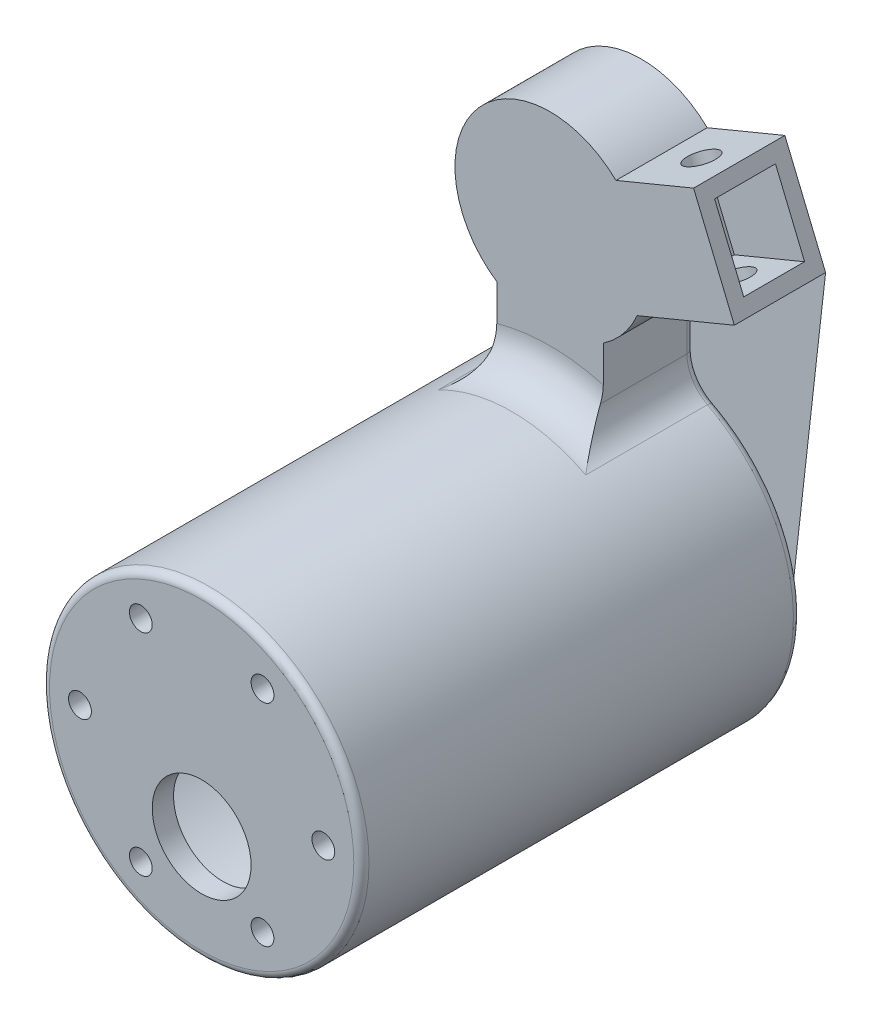
SolidWorks part; units mm, degrees
ref_plane "Front Plane" through (0, 0, 0) normal (0, 0, 1) x (1, 0, 0)
ref_plane "Top Plane" through (0, 0, 0) normal (0, 1, 0) x (1, 0, 0)
ref_plane "Right Plane" through (0, 0, 0) normal (1, 0, 0) x (0, 0, -1)
sketch "Sketch1" plane through (0, 0, 0) normal (0, 0, 1) x (1, 0, 0)
  line L0 (0, 0) -> (-12.5, 0) construction
  line L1 (0, 0) -> (-11.5485, -4.7835) construction
  line L2 (24.2314, 0.2955) -> (11.4585, -4.9953)
  line L3 (0, 0) -> (0, 10) construction
  line L4 (20.7873, 8.6104) -> (24.2314, 0.2955)
  line L5 (20.7873, 8.6104) -> (18.8739, 13.2298)
  line L6 (18.8739, 13.2298) -> (8.671, 9.0036)
  line L8 (0, 0) -> (0, -15.9469) construction
  line L9 (0, -15.9469) -> (-7, -15.9469) construction
  line L12 (-20.7873, -8.6104) -> (-11.5485, -4.7835) construction
  line L15 (0, -15.9469) -> (7, -15.9469) construction
  line L16 (-20.7873, 8.6104) -> (-18.8739, 13.2298)
  line L17 (7, -10.3562) -> (7, -20.3562)
  line L18 (7, -20.3562) -> (-7, -20.3562)
  line L19 (-7, -20.3562) -> (-7, -10.3562)
  line L20 (-18.8739, 13.2298) -> (-8.671, 9.0036)
  line L21 (-20.7873, 8.6104) -> (-24.2314, 0.2955)
  line L22 (-24.2314, 0.2955) -> (-11.4585, -4.9953)
  circle A3 centre (0, 0) radius 12.5
  circle A4 centre (0, 0) radius 10
  dimension "D1" = 25
  dimension "D3" = 22.5
  dimension "D2" = 20
  dimension "D4" = 10
  dimension "D5" = 14
  dimension "D6" = 10
extrude "Boss-Extrude2" add sketch "Sketch1" along normal blind 12 contours A3
sketch "Sketch2" plane through (0, 0, 0) normal (0, 0, 1) x (1, 0, 0)
  line L0 (24.2314, 0.2955) -> (11.4585, -4.9953) construction
  line L1 (20.7873, 8.6104) -> (24.2314, 0.2955) construction
  line L2 (20.7873, 8.6104) -> (18.8739, 13.2298) construction
  line L3 (18.8739, 13.2298) -> (8.671, 9.0036) construction
  line L4 (24.2314, 0.2955) -> (11.4585, -4.9953)
  line L5 (20.7873, 8.6104) -> (24.2314, 0.2955)
  line L6 (20.7873, 8.6104) -> (18.8739, 13.2298)
  line L7 (18.8739, 13.2298) -> (8.671, 9.0036)
  line L8 (7, -10.3562) -> (7, -20.3562) construction
  line L9 (7, -20.3562) -> (-7, -20.3562) construction
  line L10 (-7, -20.3562) -> (-7, -10.3562) construction
  line L11 (7, -10.3562) -> (7, -20.3562)
  line L12 (7, -20.3562) -> (-7, -20.3562)
  line L13 (-7, -20.3562) -> (-7, -10.3562)
  circle A0 centre (0, 0) radius 12.5 construction
  arc A2 (-7, -10.3562) -> (7, -10.3562) centre (0, 0) ccw
  arc A3 (11.4585, -4.9953) -> (8.671, 9.0036) centre (0, 0) ccw
extrude "Boss-Extrude3" add sketch "Sketch2" along normal blind 12
sketch "Sketch3" plane through (20.7873, 8.6104, 0) normal (0.9239, 0.3827, 0) x (0, 0, -1)
  line L0 (-12, 5) -> (0, 5) construction
  line L1 (-10, 3) -> (-2, 3)
  line L2 (-10, 3) -> (-10, -7)
  line L3 (-10, -7) -> (-2, -7)
  line L4 (-2, 3) -> (-2, -7)
  line L5 (-12, -9) -> (0, -9) construction
  line L6 (0, -9) -> (0, 5) construction
  line L7 (-12, -9) -> (-12, 5) construction
  dimension "D1" = 2
  dimension "D2" = 2
  dimension "D3" = 2
  dimension "D4" = 2
extrude "Cut-Extrude1" cut sketch "Sketch3" against normal blind 10
sketch "Sketch4" plane through (-1.9134, 4.6194, 0) normal (-0.3827, 0.9239, 0) x (0.9239, 0.3827, 0)
  line L0 (11.4564, -6) -> (22.5, -6) construction
  line L5 (16.9782, 0) -> (16.9782, -12) construction
  circle A0 centre (17.1192, -6) radius 2
extrude "Cut-Extrude2" cut sketch "Sketch4" against normal through all
sketch "Sketch5" plane through (0, 0, 0) normal (0, 0, 1) x (1, 0, 0)
  line L0 (0, -20.3562) -> (0, -40.1562) construction
  line L1 (-7, -20.3562) -> (7, -20.3562) construction
  circle A0 centre (0, -40.1562) radius 21.001
  dimension "D2" = 42.0019
  dimension "D1" = 19.8
extrude "Boss-Extrude4" add sketch "Sketch5" along normal blind 57.8
sketch "Sketch6" plane through (0, 0, 0) normal (0, 0, -1) x (-1, 0, 0)
  line L0 (0, -61.1571) -> (0, -40.1562) construction
  arc A0 (-7, -20.3562) -> (7, -20.3562) centre (0, -40.1562) ccw construction
  circle A1 centre (0, -40.1562) radius 19
  dimension "D1" = 38
extrude "Cut-Extrude3" cut sketch "Sketch6" against normal blind 55
sketch "Sketch7" plane through (0, 0, 57.8) normal (0, 0, 1) x (1, 0, 0)
  line L0 (-21.001, -40.1562) -> (21.001, -40.1562) construction
  line L1 (0, -40.1562) -> (0, -47.1562) construction
  line L2 (-19, -40.1562) -> (-16, -40.1562) construction
  circle A0 centre (0, -40.1562) radius 21.001 construction
  circle A2 centre (0, -47.1562) radius 6.5
  circle A3 centre (-16, -40.1562) radius 1.5
  circle A5 centre (-8, -54.0126) radius 1.5
  circle A6 centre (8, -54.0126) radius 1.5
  circle A7 centre (16, -40.1562) radius 1.5
  circle A8 centre (8, -26.2998) radius 1.5
  circle A9 centre (-8, -26.2998) radius 1.5
  point P28 (0, -40.1562)
  dimension "D1" = 7
  dimension "D2" = 6
extrude "Cut-Extrude4" cut sketch "Sketch7" against normal through all
fillet "Fillet1" radius 5 3 edges at (7, -20.3562, 6) (-7, -20.3562, 6) (0, -19.1552, 12)
fillet "Fillet2" radius 1 7 edges at (-19, -40.1562, 0) (-7, -13.7231, 0) (-7.7258, -19.6844, 0) (7, -13.7231, 0) (7.7258, -19.6844, 0) (21.001, -40.1562, 57.8) (0, -61.1571, 0)
